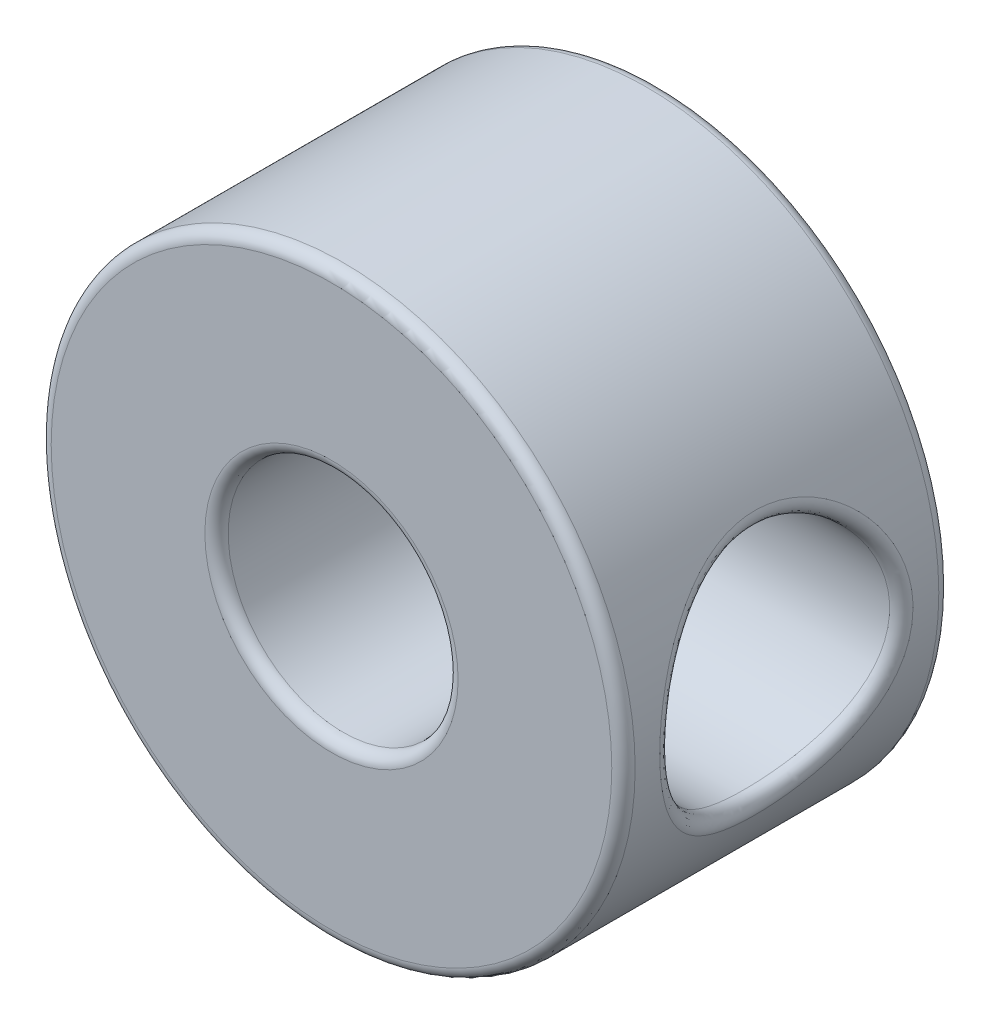
SolidWorks part; units mm, degrees
ref_plane "Front Plane" through (0, 0, 0) normal (0, 0, 1) x (1, 0, 0)
ref_plane "Top Plane" through (0, 0, 0) normal (0, 1, 0) x (1, 0, 0)
ref_plane "Right Plane" through (0, 0, 0) normal (1, 0, 0) x (0, 0, -1)
sketch "Sketch2" plane through (0, 0, 0) normal (0, 0, 1) x (1, 0, 0)
  circle A0 centre (0, 0) radius 6.35
  dimension "D1" = 12.7
extrude "Boss-Extrude1" add sketch "Sketch2" along normal blind 7.112
sketch "Sketch3" plane through (0, 0, 7.112) normal (0, 0, 1) x (1, 0, 0)
  circle A0 centre (0, 0) radius 2.5
  dimension "D1" = 5
extrude "Cut-Extrude1" cut sketch "Sketch3" against normal blind 19.05 contours A0
sketch "Sketch4" plane through (0, 0, 0) normal (1, 0, 0) x (0, 0, -1)
  circle A0 centre (-3.5687, 0) radius 2.5
  dimension "D1" = 5
  dimension "D2" = 3.5687
extrude "Cut-Extrude2" cut sketch "Sketch4" along normal blind 19.05
fillet "Fillet1" radius 0.254 5 edges at (2.5, 0, 0) (6.35, 0, 0) (6.3393, 0.3688, 1.096) (2.5, 0, 7.112) (6.35, 0, 7.112)
